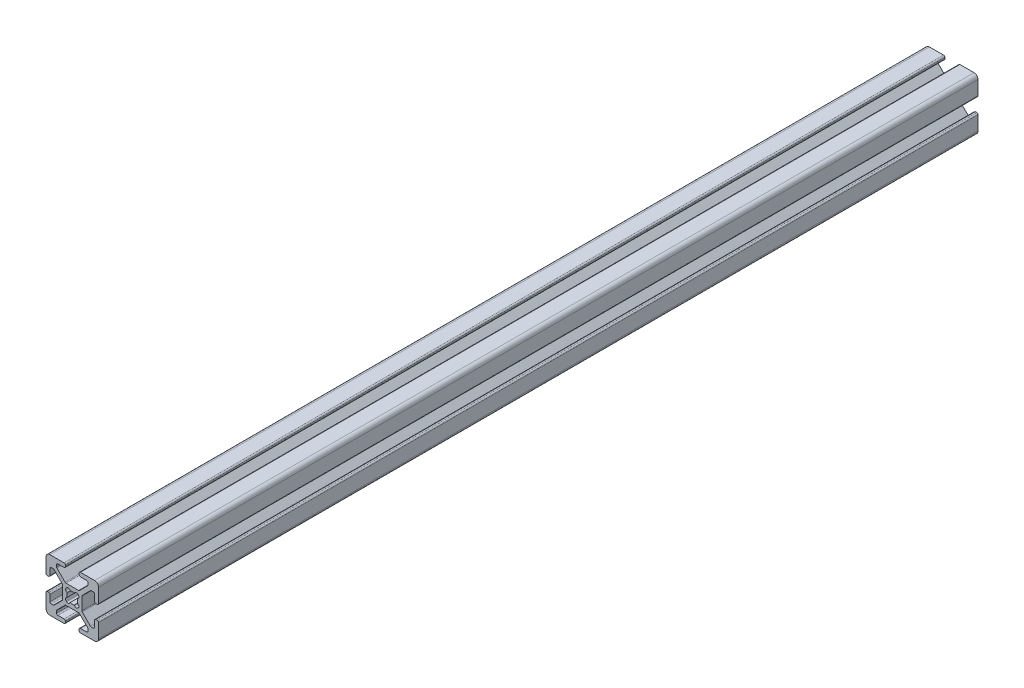
SolidWorks part; units mm, degrees
material "6105-T5 Aluminum"
ref_plane "Front Plane" through (0, 0, 0) normal (0, 0, 1) x (1, 0, 0)
ref_plane "Top Plane" through (0, 0, 0) normal (0, 1, 0) x (1, 0, 0)
ref_plane "Right Plane" through (0, 0, 0) normal (1, 0, 0) x (0, 0, -1)
sketch "Sketch1" plane through (0, 0, 0) normal (0, 0, 1) x (1, 0, 0)
  line L0 (9.492, 2.63) -> (9.008, 2.63)
  line L1 (8.5, 3.138) -> (8.5, 5.487)
  line L2 (10, 3.138) -> (10, 8.5)
  line L3 (3.655, -2.3839) -> (3.655, 2.3839)
  line L4 (7.2661, 5.995) -> (7.992, 5.995)
  line L5 (6.9069, 5.8462) -> (3.8038, 2.7431)
  line L6 (9.492, -2.63) -> (9.008, -2.63)
  line L7 (10, -3.138) -> (10, -8.5)
  line L8 (8.5, -3.138) -> (8.5, -5.487)
  line L9 (7.2661, -5.995) -> (7.992, -5.995)
  line L10 (6.9069, -5.8462) -> (3.8038, -2.7431)
  line L11 (2.1249, -2.3045) -> (2.3045, -2.1249)
  line L12 (-2.63, 9.492) -> (-2.63, 9.008)
  line L13 (-3.138, 10) -> (-8.5, 10)
  line L14 (-3.138, 8.5) -> (-5.487, 8.5)
  line L15 (2.3839, 3.655) -> (-2.3839, 3.655)
  line L16 (-5.995, 7.2661) -> (-5.995, 7.992)
  line L17 (-5.8462, 6.9069) -> (-2.7431, 3.8038)
  line L18 (2.63, 9.492) -> (2.63, 9.008)
  line L19 (3.138, 10) -> (8.5, 10)
  line L20 (3.138, 8.5) -> (5.487, 8.5)
  line L21 (5.995, 7.2661) -> (5.995, 7.992)
  line L22 (5.8462, 6.9069) -> (2.7431, 3.8038)
  line L23 (2.3045, 2.1249) -> (2.1249, 2.3045)
  line L24 (-9.492, -2.63) -> (-9.008, -2.63)
  line L25 (-10, -3.138) -> (-10, -8.5)
  line L26 (-8.5, -3.138) -> (-8.5, -5.487)
  line L27 (-3.655, 2.3839) -> (-3.655, -2.3839)
  line L28 (-7.2661, -5.995) -> (-7.992, -5.995)
  line L29 (-6.9069, -5.8462) -> (-3.8038, -2.7431)
  line L30 (-9.492, 2.63) -> (-9.008, 2.63)
  line L31 (-10, 3.138) -> (-10, 8.5)
  line L32 (-8.5, 3.138) -> (-8.5, 5.487)
  line L33 (-7.2661, 5.995) -> (-7.992, 5.995)
  line L34 (-6.9069, 5.8462) -> (-3.8038, 2.7431)
  line L35 (-2.1249, 2.3045) -> (-2.3045, 2.1249)
  line L36 (2.63, -9.492) -> (2.63, -9.008)
  line L37 (3.138, -10) -> (8.5, -10)
  line L38 (3.138, -8.5) -> (5.487, -8.5)
  line L39 (-2.3839, -3.655) -> (2.3839, -3.655)
  line L40 (5.995, -7.2661) -> (5.995, -7.992)
  line L41 (5.8462, -6.9069) -> (2.7431, -3.8038)
  line L42 (-2.63, -9.492) -> (-2.63, -9.008)
  line L43 (-3.138, -10) -> (-8.5, -10)
  line L44 (-3.138, -8.5) -> (-5.487, -8.5)
  line L45 (-5.995, -7.2661) -> (-5.995, -7.992)
  line L46 (-5.8462, -6.9069) -> (-2.7431, -3.8038)
  line L47 (-2.3045, -2.1249) -> (-2.1249, -2.3045)
  arc A0 (-0.804, -1.9351) -> (0.804, -1.9351) centre (0, 0) ccw
  arc A1 (8.5, 5.487) -> (7.992, 5.995) centre (7.992, 5.487) ccw
  arc A2 (7.2661, 5.995) -> (6.9069, 5.8462) centre (7.2661, 5.487) ccw
  arc A3 (3.8038, 2.7431) -> (3.655, 2.3839) centre (4.163, 2.3839) ccw
  arc A4 (3.655, -2.3839) -> (3.8038, -2.7431) centre (4.163, -2.3839) ccw
  arc A5 (6.9069, -5.8462) -> (7.2661, -5.995) centre (7.2661, -5.487) ccw
  arc A6 (7.992, -5.995) -> (8.5, -5.487) centre (7.992, -5.487) ccw
  arc A7 (9.008, -2.63) -> (8.5, -3.138) centre (9.008, -3.138) ccw
  arc A8 (10, -3.138) -> (9.492, -2.63) centre (9.492, -3.138) ccw
  arc A9 (9.492, 2.63) -> (10, 3.138) centre (9.492, 3.138) ccw
  arc A10 (8.5, 3.138) -> (9.008, 2.63) centre (9.008, 3.138) ccw
  arc A11 (0.804, -1.9351) -> (2.1249, -2.3045) centre (1.5684, -1.748) ccw
  arc A12 (2.3045, -2.1249) -> (1.9351, -0.804) centre (1.748, -1.5684) ccw
  arc A13 (-2.63, 9.492) -> (-3.138, 10) centre (-3.138, 9.492) ccw
  arc A14 (-3.138, 8.5) -> (-2.63, 9.008) centre (-3.138, 9.008) ccw
  arc A15 (1.9351, -0.804) -> (1.9351, 0.804) centre (0, 0) ccw
  arc A16 (-2.7431, 3.8038) -> (-2.3839, 3.655) centre (-2.3839, 4.163) ccw
  arc A17 (-5.487, 8.5) -> (-5.995, 7.992) centre (-5.487, 7.992) ccw
  arc A18 (-5.995, 7.2661) -> (-5.8462, 6.9069) centre (-5.487, 7.2661) ccw
  arc A19 (2.63, 9.008) -> (3.138, 8.5) centre (3.138, 9.008) ccw
  arc A20 (3.138, 10) -> (2.63, 9.492) centre (3.138, 9.492) ccw
  arc A21 (5.995, 7.992) -> (5.487, 8.5) centre (5.487, 7.992) ccw
  arc A22 (5.8462, 6.9069) -> (5.995, 7.2661) centre (5.487, 7.2661) ccw
  arc A23 (2.3839, 3.655) -> (2.7431, 3.8038) centre (2.3839, 4.163) ccw
  arc A24 (1.9351, 0.804) -> (2.3045, 2.1249) centre (1.748, 1.5684) ccw
  arc A25 (2.1249, 2.3045) -> (0.804, 1.9351) centre (1.5684, 1.748) ccw
  arc A26 (-9.492, -2.63) -> (-10, -3.138) centre (-9.492, -3.138) ccw
  arc A27 (-8.5, -3.138) -> (-9.008, -2.63) centre (-9.008, -3.138) ccw
  arc A28 (0.804, 1.9351) -> (-0.804, 1.9351) centre (0, 0) ccw
  arc A29 (-3.8038, -2.7431) -> (-3.655, -2.3839) centre (-4.163, -2.3839) ccw
  arc A30 (-8.5, -5.487) -> (-7.992, -5.995) centre (-7.992, -5.487) ccw
  arc A31 (-7.2661, -5.995) -> (-6.9069, -5.8462) centre (-7.2661, -5.487) ccw
  arc A32 (-9.008, 2.63) -> (-8.5, 3.138) centre (-9.008, 3.138) ccw
  arc A33 (-10, 3.138) -> (-9.492, 2.63) centre (-9.492, 3.138) ccw
  arc A34 (-7.992, 5.995) -> (-8.5, 5.487) centre (-7.992, 5.487) ccw
  arc A35 (-6.9069, 5.8462) -> (-7.2661, 5.995) centre (-7.2661, 5.487) ccw
  arc A36 (-3.655, 2.3839) -> (-3.8038, 2.7431) centre (-4.163, 2.3839) ccw
  arc A37 (-0.804, 1.9351) -> (-2.1249, 2.3045) centre (-1.5684, 1.748) ccw
  arc A38 (-2.3045, 2.1249) -> (-1.9351, 0.804) centre (-1.748, 1.5684) ccw
  arc A39 (2.63, -9.492) -> (3.138, -10) centre (3.138, -9.492) ccw
  arc A40 (3.138, -8.5) -> (2.63, -9.008) centre (3.138, -9.008) ccw
  arc A41 (-1.9351, 0.804) -> (-1.9351, -0.804) centre (0, 0) ccw
  arc A42 (2.7431, -3.8038) -> (2.3839, -3.655) centre (2.3839, -4.163) ccw
  arc A43 (5.487, -8.5) -> (5.995, -7.992) centre (5.487, -7.992) ccw
  arc A44 (5.995, -7.2661) -> (5.8462, -6.9069) centre (5.487, -7.2661) ccw
  arc A45 (-2.63, -9.008) -> (-3.138, -8.5) centre (-3.138, -9.008) ccw
  arc A46 (-3.138, -10) -> (-2.63, -9.492) centre (-3.138, -9.492) ccw
  arc A47 (-5.995, -7.992) -> (-5.487, -8.5) centre (-5.487, -7.992) ccw
  arc A48 (-5.8462, -6.9069) -> (-5.995, -7.2661) centre (-5.487, -7.2661) ccw
  arc A49 (-2.3839, -3.655) -> (-2.7431, -3.8038) centre (-2.3839, -4.163) ccw
  arc A50 (-1.9351, -0.804) -> (-2.3045, -2.1249) centre (-1.748, -1.5684) ccw
  arc A51 (-2.1249, -2.3045) -> (-0.804, -1.9351) centre (-1.5684, -1.748) ccw
  arc A52 (10, 8.5) -> (8.5, 10) centre (8.5, 8.5) ccw
  arc A53 (8.5, -10) -> (10, -8.5) centre (8.5, -8.5) ccw
  arc A54 (-10, -8.5) -> (-8.5, -10) centre (-8.5, -8.5) ccw
  arc A55 (-8.5, 10) -> (-10, 8.5) centre (-8.5, 8.5) ccw
extrude "Extrude1" add sketch "Sketch1" against normal blind 335
